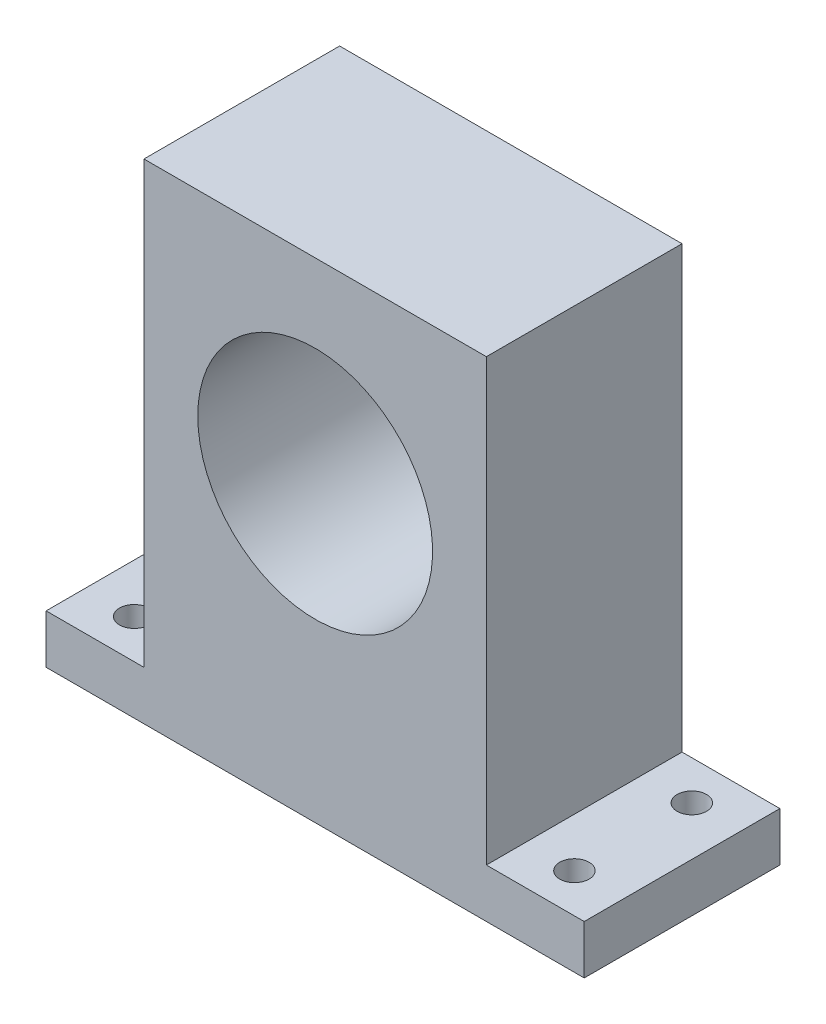
SolidWorks part; units mm, degrees
ref_plane "Front" through (0, 0, 0) normal (0, 0, 1) x (1, 0, 0)
ref_plane "Top" through (0, 0, 0) normal (0, 1, 0) x (1, 0, 0)
ref_plane "Right" through (0, 0, 0) normal (1, 0, 0) x (0, 0, -1)
sketch "Эскиз1" plane through (0, 0, 0) normal (0, 0, 1) x (1, 0, 0)
  line L1 (-17.5, 25) -> (17.5, 25)
  line L2 (-17.5, 25) -> (-17.5, -25)
  line L3 (-17.5, -25) -> (17.5, -25)
  line L4 (17.5, 25) -> (17.5, -25)
  line L5 (-17.5, 25) -> (17.5, -25) construction
  line L6 (-17.5, -25) -> (17.5, 25) construction
  point P0 (0, 0)
  dimension "D1" = 35
  dimension "D2" = 50
extrude "Бобышка-Вытянуть1" add sketch "Эскиз1" along normal blind 20
sketch "Эскиз2" plane through (17.5, 0, 0) normal (1, 0, 0) x (0, 0, -1)
  line L0 (0, -25) -> (0, 25) construction
  line L1 (-20, -25) -> (0, -25)
  line L2 (-20, -25) -> (-20, -20)
  line L3 (-20, -20) -> (0, -20)
  line L4 (0, -25) -> (0, -20)
  dimension "D1" = 5
extrude "Бобышка-Вытянуть2" add sketch "Эскиз2" along normal blind 10
sketch "Эскиз3" plane through (-17.5, 0, 0) normal (-1, 0, 0) x (0, 0, 1)
  line L0 (20, 25) -> (20, -25) construction
  line L1 (0, -25) -> (20, -25)
  line L2 (0, -25) -> (0, -20)
  line L3 (0, -20) -> (20, -20)
  line L4 (20, -25) -> (20, -20)
  dimension "D1" = 5
extrude "Бобышка-Вытянуть3" add sketch "Эскиз3" along normal blind 10
sketch "Эскиз4" plane through (0, 0, 0) normal (0, 0, -1) x (-1, 0, 0)
  line L0 (27.5, -25) -> (-27.5, -25) construction
  line L1 (17.5, 25) -> (17.5, -20) construction
  circle A0 centre (0, 5) radius 12
  dimension "D2" = 24
  dimension "D1" = 30
  dimension "D3" = 17.5
extrude "Вырез-Вытянуть1" cut sketch "Эскиз4" against normal blind 20
sketch "Эскиз5" plane through (0, -20, 0) normal (0, 1, 0) x (1, 0, 0)
  line L0 (-27.5, -20) -> (-27.5, 0) construction
  line L1 (-27.5, 0) -> (-17.5, 0) construction
  circle A0 centre (-22.5, -4) radius 1.5
  dimension "D3" = 3
  dimension "D1" = 5
  dimension "D2" = 4
extrude "Вырез-Вытянуть2" cut sketch "Эскиз5" against normal blind 5
sketch "Эскиз6" plane through (0, -20, 0) normal (0, 1, 0) x (1, 0, 0)
  line L0 (-27.5, -20) -> (-27.5, 0) construction
  line L1 (-27.5, -20) -> (-17.5, -20) construction
  circle A0 centre (-22.5, -16) radius 1.5
  point P4 (0, 0)
  dimension "D3" = 3
  dimension "D1" = 5
  dimension "D2" = 4
extrude "Вырез-Вытянуть3" cut sketch "Эскиз6" against normal blind 5
sketch "Эскиз7" plane through (0, -20, 0) normal (0, 1, 0) x (1, 0, 0)
  line L0 (27.5, 0) -> (27.5, -20) construction
  line L1 (27.5, 0) -> (17.5, 0) construction
  circle A0 centre (22.5, -4) radius 1.5
  dimension "D1" = 3
  dimension "D2" = 5
  dimension "D3" = 4
extrude "Вырез-Вытянуть4" cut sketch "Эскиз7" against normal blind 5
sketch "Эскиз8" plane through (0, -20, 0) normal (0, 1, 0) x (1, 0, 0)
  line L0 (27.5, -20) -> (17.5, -20) construction
  line L1 (27.5, 0) -> (27.5, -20) construction
  circle A0 centre (22.5, -16) radius 1.5
  dimension "D1" = 3
  dimension "D2" = 4
  dimension "D3" = 5
extrude "Вырез-Вытянуть5" cut sketch "Эскиз8" against normal blind 5
